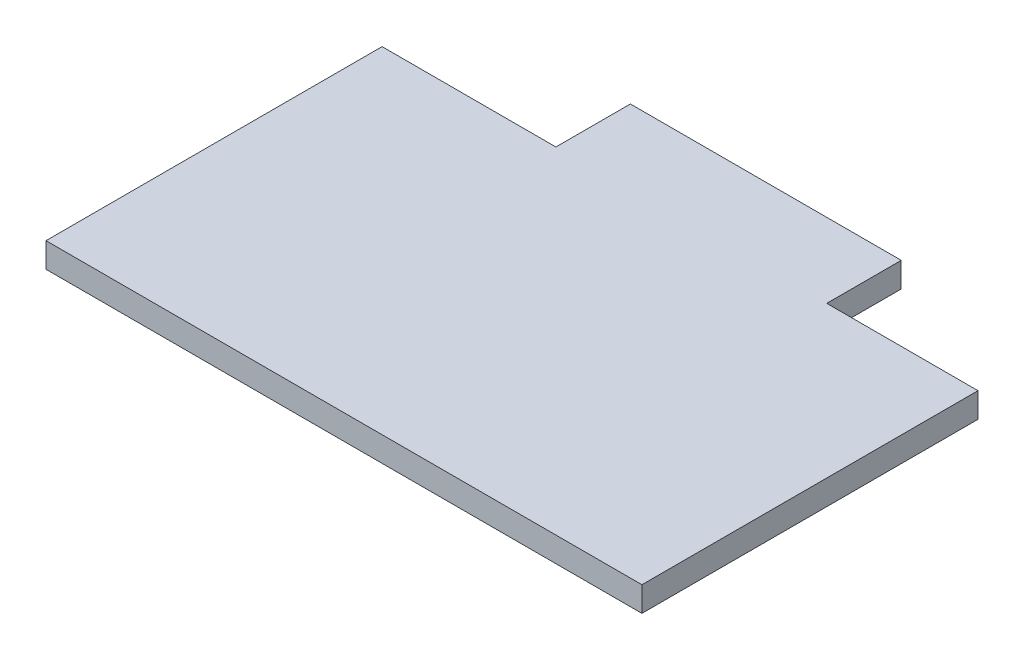
SolidWorks part; units mm, degrees
ref_plane "Front Plane" through (0, 0, 0) normal (0, 0, 1) x (1, 0, 0)
ref_plane "Top Plane" through (0, 0, 0) normal (0, 1, 0) x (1, 0, 0)
ref_plane "Right Plane" through (0, 0, 0) normal (1, 0, 0) x (0, 0, -1)
sketch "Sketch1" plane through (0, 0, 0) normal (0, 1, 0) x (1, 0, 0)
  line L1 (-152.4, -105) -> (152.4, -105)
  line L2 (-152.4, -105) -> (-152.4, 105)
  line L3 (-152.4, 105) -> (152.4, 105)
  line L4 (152.4, -105) -> (152.4, 105)
  line L5 (-152.4, -105) -> (152.4, 105) construction
  line L6 (-152.4, 105) -> (152.4, -105) construction
  point P0 (0, 0)
  dimension "D1" = 304.8
  dimension "D2" = 210
extrude "Boss-Extrude1" add sketch "Sketch1" along normal blind 12.7
sketch "Sketch2" plane through (0, 0, 0) normal (0, -1, 0) x (1, 0, 0)
  line L0 (-152.4, -105) -> (-152.4, 105) construction
  line L1 (-63.5, -66.9) -> (-167.3261, -66.9)
  line L2 (-63.5, -66.9) -> (-63.5, -142.3041)
  line L3 (-63.5, -142.3041) -> (-167.3261, -142.3041)
  line L4 (-167.3261, -66.9) -> (-167.3261, -142.3041)
  line L5 (75.0369, -142.3041) -> (180.9109, -142.3041)
  line L6 (75.0369, -142.3041) -> (75.0369, -66.9)
  line L7 (75.0369, -66.9) -> (180.9109, -66.9)
  line L8 (180.9109, -142.3041) -> (180.9109, -66.9)
  line L9 (152.4, -105) -> (-152.4, -105) construction
  dimension "D1" = 88.9
  dimension "D2" = 38.1
extrude "Cut-Extrude1" cut sketch "Sketch2" against normal blind 121
sketch "Sketch3" plane through (0, 12.7, 0) normal (0, 1, 0) x (1, 0, 0)
  point P0 (-40.018, 89)
  point P1 (-32.018, 97)
  point P3 (-32.018, 81)
  point P5 (-24.018, 89)
  point P7 (23.982, 89)
  point P9 (31.982, 97)
  point P11 (31.982, 81)
  point P13 (39.982, 89)
sketch "Sketch4" plane through (0, 12.7, 0) normal (0, 1, 0) x (1, 0, 0)
  line L0 (-152.4, 66.9) -> (-152.4, -105) construction
  line L1 (-63.5, 66.9) -> (-152.4, 66.9) construction
  line L2 (152.4, -105) -> (152.4, 66.9) construction
  point P0 (-95.53, -6.88)
  point P1 (-87.53, 1.12)
  point P2 (-79.53, -6.88)
  point P3 (-87.53, -14.88)
  point P4 (55.45, -6.88)
  point P5 (63.45, 1.12)
  point P6 (71.45, -6.88)
  point P7 (63.45, -14.88)
  point P12 (146.05, 59.68)
  point P14 (-146.05, 59.68)
  dimension "D1" = 8
  dimension "D2" = 16
  dimension "D3" = 8
  dimension "D4" = 16
  dimension "D5" = 56.87
  dimension "D6" = 73.78
  dimension "D7" = 134.98
  dimension "D8" = 16
  dimension "D9" = 8
  dimension "D10" = 16
  dimension "D11" = 8
  dimension "D12" = 7.22
  dimension "D13" = 6.35
  dimension "D14" = 6.35
